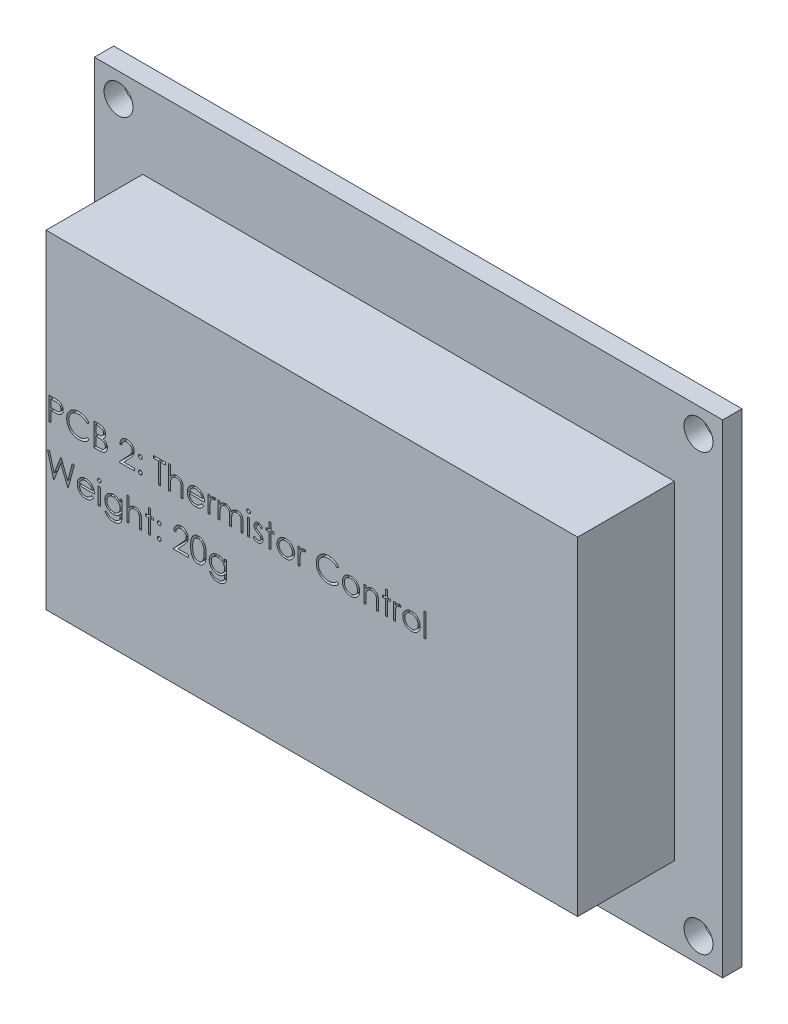
SolidWorks part; units mm, degrees
ref_plane "Front Plane" through (0, 0, 0) normal (0, 0, 1) x (1, 0, 0)
ref_plane "Top Plane" through (0, 0, 0) normal (0, 1, 0) x (1, 0, 0)
ref_plane "Right Plane" through (0, 0, 0) normal (1, 0, 0) x (0, 0, -1)
sketch "Sketch1" plane through (0, 0, 0) normal (0, 0, 1) x (1, 0, 0)
  line L0 (-32.5, 25) -> (32.5, 25)
  line L1 (-32.5, 25) -> (-32.5, -25)
  line L2 (-32.5, -25) -> (32.5, -25)
  line L3 (32.5, 25) -> (32.5, -25)
  line L4 (0, -25) -> (0, 25) construction
  line L5 (-32.5, 0) -> (32.5, 0) construction
  line L6 (-30, -22.5) -> (30, -22.5)
  line L7 (-30, -22.5) -> (-30, 22.5)
  line L8 (-30, 22.5) -> (30, 22.5)
  line L9 (30, -22.5) -> (30, 22.5)
  line L10 (-30, -22.5) -> (30, 22.5) construction
  line L11 (-30, 22.5) -> (30, -22.5) construction
  circle A0 centre (-30, 22.5) radius 1.5
  circle A1 centre (-30, -22.5) radius 1.5
  circle A2 centre (30, -22.5) radius 1.5
  circle A3 centre (30, 22.5) radius 1.5
  point P4 (0, 0)
  point P17 (0, 0)
  dimension "D5" = 3
  dimension "D6" = 3
  dimension "D7" = 3
  dimension "D8" = 3
  dimension "D1" = 50
  dimension "D2" = 65
  dimension "D3" = 2.5
  dimension "D4" = 2.5
extrude "Boss-Extrude1" add sketch "Sketch1" along normal blind 2 contours A3 L8 A0 L7 A1 L6 A2 L9 | L3 L0 L1 L2 A3 L9 A2 L6 A1 L7 A0 L8
sketch "Sketch2" plane through (0, 0, 2) normal (0, 0, 1) x (1, 0, 0)
  line L0 (-32.5, 25) -> (32.5, 25) construction
  line L1 (-27.5, -17) -> (27.5, -17)
  line L2 (-27.5, -17) -> (-27.5, 17)
  line L3 (-27.5, 17) -> (27.5, 17)
  line L4 (27.5, -17) -> (27.5, 17)
  line L5 (-27.5, -17) -> (27.5, 17) construction
  line L6 (-27.5, 17) -> (27.5, -17) construction
  line L7 (-32.5, 25) -> (-32.5, -25) construction
  point P0 (0, 0)
  dimension "D1" = 8
  dimension "D2" = 5
extrude "Boss-Extrude2" add sketch "Sketch2" along normal blind 10
sketch "Sketch3" plane through (0, 0, 12) normal (0, 0, 1) x (1, 0, 0)
  line L0 (-27.5, 0) -> (27.5, 0) construction
  line L1 (-27.5, 17) -> (-27.5, -17) construction
  line L2 (27.5, -17) -> (27.5, 17) construction
  text T0 "PCB 2: Thermistor Control\r\nWeight: 20g" font "Century Gothic" height in points 9
  point P7 (0, 0)
  point P8 (0, 0)
  point P9 (6.2416, -2.9049)
  dimension "D1" = 27.5
  dimension "D2" = 27.5
extrude "Cut-Extrude1" cut sketch "Sketch3" against normal blind 2
